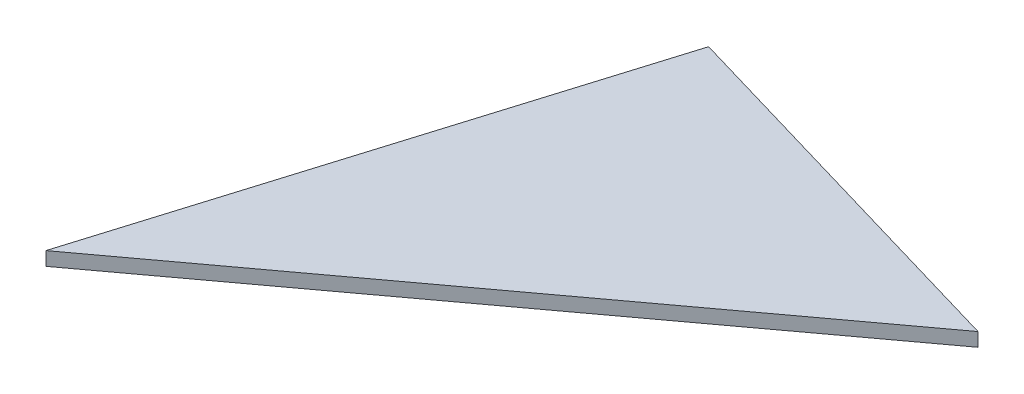
SolidWorks part; units mm, degrees
ref_plane "Plan de face" through (0, 0, 0) normal (0, 0, 1) x (1, 0, 0)
ref_plane "Plan de dessus" through (0, 0, 0) normal (0, 1, 0) x (1, 0, 0)
ref_plane "Plan de droite" through (0, 0, 0) normal (1, 0, 0) x (0, 0, -1)
sketch "Esquisse1" plane through (0, 0, 0) normal (0, 1, 0) x (1, 0, 0)
  line L0 (22.672, 74.4089) -> (0, 0)
  line L1 (0, 0) -> (78.5427, 58.0022)
  line L2 (78.5427, 58.0022) -> (22.672, 74.4089)
  point P3 (0, 0)
extrude "Boss.-Extru.1" add sketch "Esquisse1" along normal blind 2
